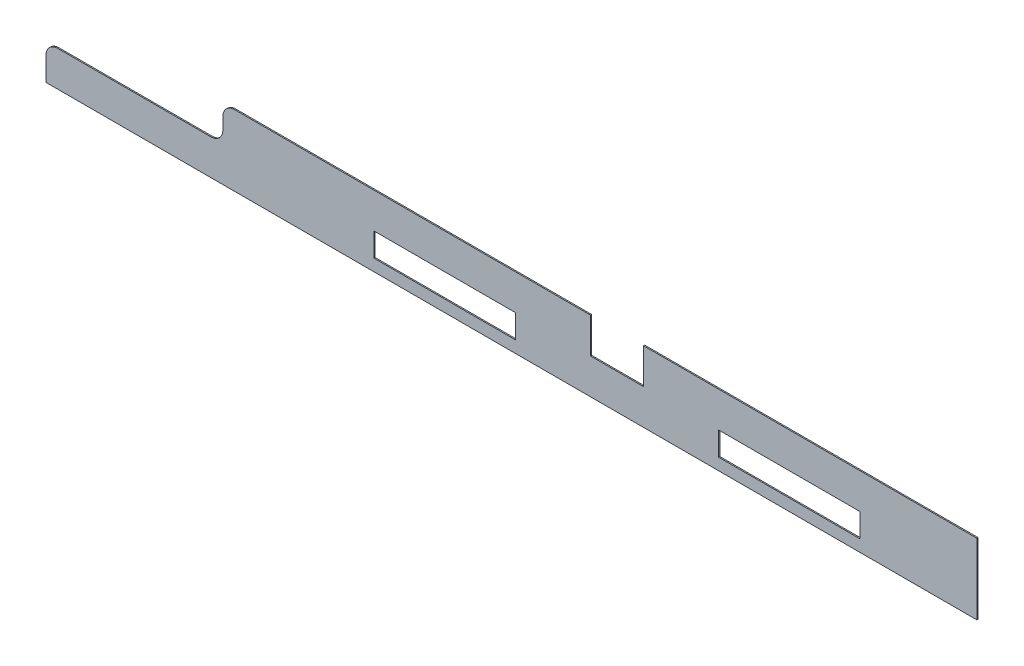
SolidWorks part; units mm, degrees
material "Acier non allié"
ref_plane "Plan de face" through (0, 0, 0) normal (0, 0, 1) x (1, 0, 0)
ref_plane "Plan de dessus" through (0, 0, 0) normal (0, 1, 0) x (1, 0, 0)
ref_plane "Plan de droite" through (0, 0, 0) normal (1, 0, 0) x (0, 0, -1)
sketch "Esquisse1" plane through (0, 0, 0) normal (0, 0, 1) x (1, 0, 0)
  line L0 (-610.5, 0) -> (610.5, 0)
  line L1 (610.5, 0) -> (610.5, 120)
  line L2 (610.5, 120) -> (45, 120)
  line L3 (45, 120) -> (45, 60)
  line L4 (45, 60) -> (-45, 60)
  line L5 (-45, 60) -> (-45, 120)
  line L6 (-45, 120) -> (-610.5, 120)
  line L7 (-610.5, 120) -> (-668.6151, 120)
  line L8 (0, 0) -> (0, 60) construction
  line L9 (172.5, 20) -> (172.5, 60)
  line L10 (-412.5, 20) -> (-172.5, 20)
  line L11 (-412.5, 20) -> (-412.5, 60)
  line L12 (-412.5, 60) -> (-172.5, 60)
  line L13 (-172.5, 20) -> (-172.5, 60)
  line L14 (412.5, 20) -> (172.5, 20)
  line L15 (412.5, 20) -> (412.5, 60)
  line L16 (412.5, 60) -> (172.5, 60)
  line L17 (-668.6151, 120) -> (-668.6151, 60)
  line L18 (-668.6151, 60) -> (-968.6151, 60)
  line L19 (-968.6151, 60) -> (-968.6151, 0)
  line L20 (-968.6151, 0) -> (-610.5, 0)
  dimension "D1" = 1221
  dimension "D2" = 120
  dimension "D3" = 90
  dimension "D4" = 60
  dimension "D5" = 20
  dimension "D6" = 40
  dimension "D7" = 240
  dimension "D8" = 172.5
  dimension "D9" = 60
  dimension "D10" = 300
extrude "Boss.-Extru.1" add sketch "Esquisse1" along normal blind 2
fillet "Congé1" radius 20 3 edges at (-968.6151, 60, 1) (-668.6151, 60, 1) (-668.6151, 120, 1)
